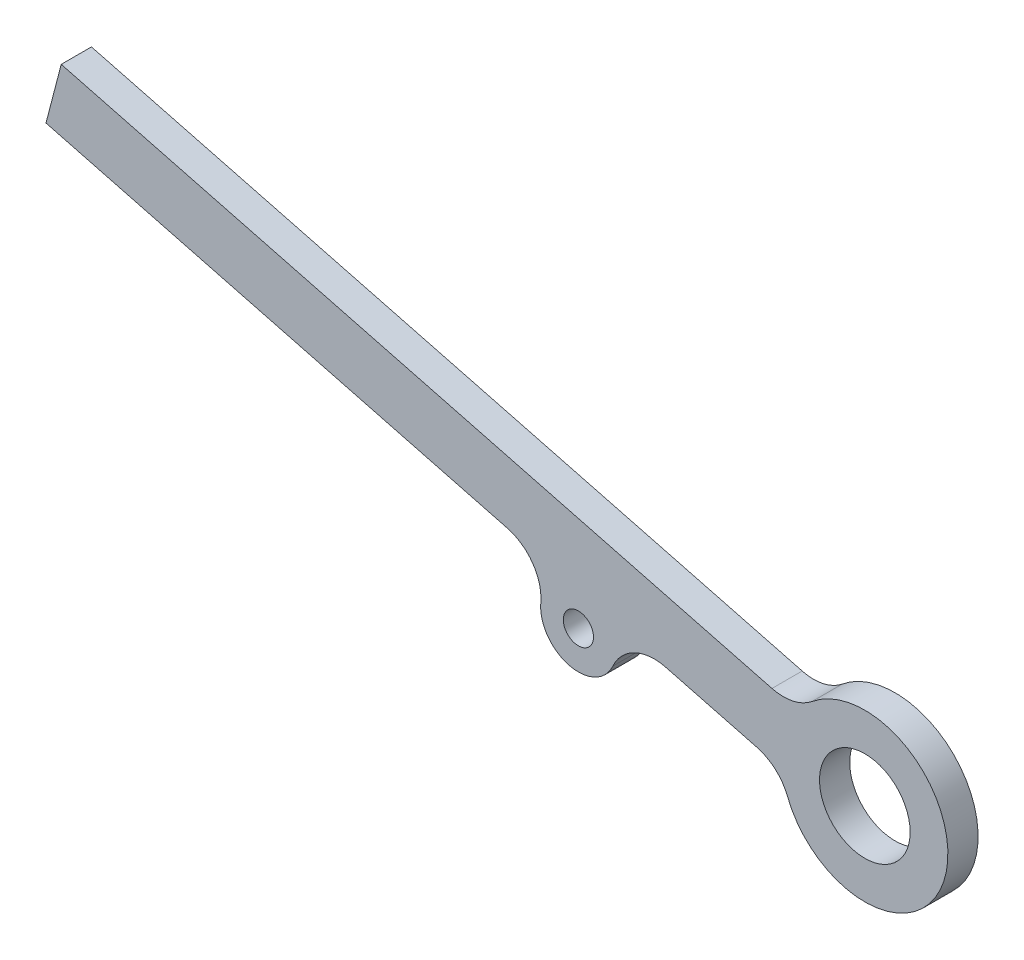
SolidWorks part; units mm, degrees
ref_plane "Front Plane" through (0, 0, 0) normal (0, 0, 1) x (1, 0, 0)
ref_plane "Top Plane" through (0, 0, 0) normal (0, 1, 0) x (1, 0, 0)
ref_plane "Right Plane" through (0, 0, 0) normal (1, 0, 0) x (0, 0, -1)
sketch "Sketch1" plane through (0, 0, 0) normal (0, 0, 1) x (1, 0, 0)
  line L0 (0, 0) -> (18.9642, -0.7027) construction
  line L1 (-277.5328, 76.5184) -> (-34.7441, 13.2853) construction
  line L2 (-277.5328, 76.5184) -> (0, 0) construction
  line L3 (11.8082, -0.9057) -> (5.7798, 0.6643)
  line L6 (-34.2401, 15.2208) -> (-35.2482, 11.3499)
  line L7 (-4.7215, 3.3993) -> (-35.2482, 11.3499)
  line L11 (12.8163, 2.9652) -> (-34.2401, 15.2208)
  circle A0 centre (0, 0) radius 1
  circle A1 centre (18.9642, -0.7027) radius 3
  arc A2 (-2.4898, 0.2255) -> (2.2835, -1.0176) centre (0, 0) ccw
  arc A3 (13.8446, -2.7126) -> (15.4754, 3.5491) centre (18.9642, -0.7027) ccw
  arc A4 (-2.4898, 0.2255) -> (-4.7215, 3.3993) centre (-5.4776, 0.4962) ccw
  arc A5 (2.2835, -1.0176) -> (5.7798, 0.6643) centre (5.0237, -2.2388) cw
  arc A6 (13.8446, -2.7126) -> (11.8082, -0.9057) centre (11.052, -3.8089) ccw
  arc A7 (15.4754, 3.5491) -> (12.8163, 2.9652) centre (13.5724, 5.8683) cw
  dimension "D4" = 3
  dimension "D6" = 3
  dimension "D7" = 3
  dimension "D11" = 2
  dimension "D14" = 6
  dimension "D5" = 3
  dimension "D2" = 306.3879
  dimension "D3" = 18.9772
  dimension "D15" = 287.888
extrude "Boss-Extrude1" add sketch "Sketch1" along normal blind 2
